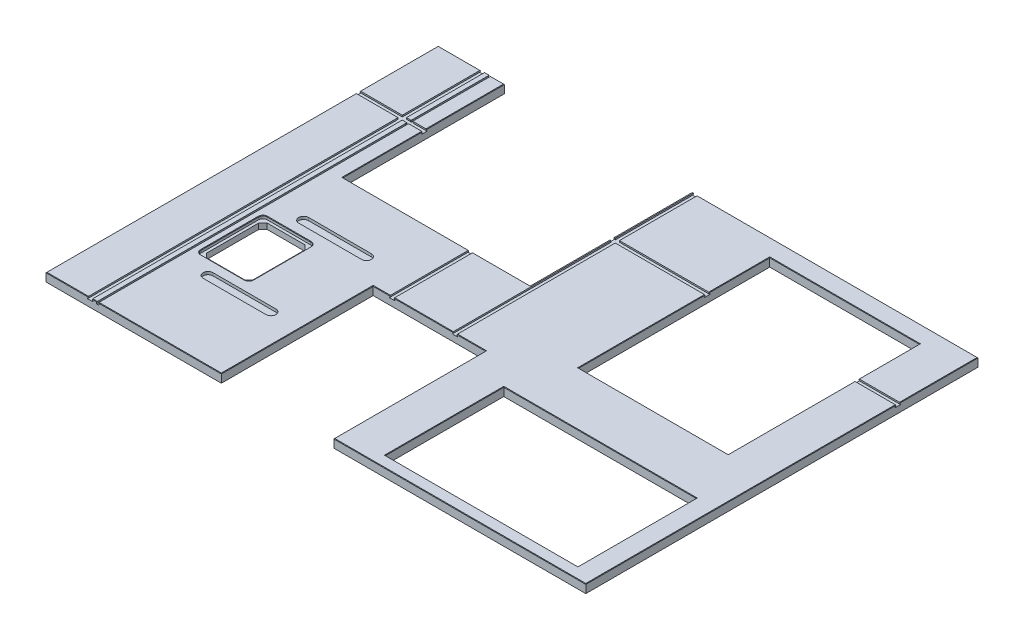
SolidWorks part; units mm, degrees
material "Oak"
ref_plane "Front Plane" through (0, 0, 0) normal (0, 0, 1) x (1, 0, 0)
ref_plane "Top Plane" through (0, 0, 0) normal (0, 1, 0) x (1, 0, 0)
ref_plane "Right Plane" through (0, 0, 0) normal (1, 0, 0) x (0, 0, -1)
sketch "Sketch1" plane through (0, 0, 0) normal (0, 1, 0) x (1, 0, 0)
  line L4 (2438.4, 0) -> (2438.4, 1771.65)
  line L5 (2438.4, 1771.65) -> (0, 1771.65)
  line L7 (0, 0) -> (2438.4, 0)
  line L8 (0, 1771.65) -> (0, 0)
  dimension "D1" = 2438.4
  dimension "D5" = 1771.65
extrude "Boss-Extrude1" add sketch "Sketch1" against normal blind 38.1
sketch "Sketch2" plane through (0, 0, 0) normal (0, 1, 0) x (1, 0, 0)
  line L1 (1482.09, 585.7875) -> (2352.04, 585.7875)
  line L2 (1482.09, 585.7875) -> (1482.09, 50.8)
  line L3 (1482.09, 50.8) -> (2352.04, 50.8)
  line L4 (2352.04, 585.7875) -> (2352.04, 50.8)
  dimension "D1" = 869.95
  dimension "D2" = 534.9875
  dimension "D3" = 1482.09
  dimension "D4" = 50.8
extrude "Cut-Extrude1" cut sketch "Sketch2" against normal through all
sketch "Sketch3" plane through (0, 0, 0) normal (0, 1, 0) x (1, 0, 0)
  line L0 (0, 0) -> (2438.4, 0) construction
  line L1 (792.1625, 685.8) -> (1300.1625, 685.8)
  line L2 (792.1625, 685.8) -> (792.1625, 0)
  line L3 (792.1625, 0) -> (1300.1625, 0)
  line L4 (1300.1625, 685.8) -> (1300.1625, 0)
  dimension "D1" = 508
  dimension "D2" = 792.1625
  dimension "D3" = 685.8
extrude "Cut-Extrude2" cut sketch "Sketch3" against normal through all
sketch "Sketch4" plane through (0, 0, 0) normal (0, 1, 0) x (1, 0, 0)
  line L1 (1576.4256, 1692.91) -> (2252.6269, 1692.91)
  line L2 (1576.4256, 1692.91) -> (1576.4256, 829.0585)
  line L3 (1576.4256, 829.0585) -> (2252.6269, 829.0585)
  line L4 (2252.6269, 1692.91) -> (2252.6269, 829.0585)
  dimension "D1" = 1576.4256
  dimension "D2" = 676.2013
  dimension "D3" = 1692.91
  dimension "D4" = 863.8515
extrude "Cut-Extrude3" cut sketch "Sketch4" against normal through all
sketch "Sketch5" plane through (0, 0, 0) normal (0, 1, 0) x (1, 0, 0)
  line L1 (299.1104, 1771.65) -> (1145.54, 1771.65)
  line L2 (299.1104, 1771.65) -> (299.1104, 1041.4)
  line L3 (299.1104, 1041.4) -> (1145.54, 1041.4)
  line L4 (1145.54, 1771.65) -> (1145.54, 1041.4)
  line L7 (2438.4, 1771.65) -> (0, 1771.65) construction
  dimension "D1" = 299.1104
  dimension "D2" = 846.4296
  dimension "D3" = 1041.4
extrude "Cut-Extrude4" cut sketch "Sketch5" against normal through all
sketch "Sketch7" plane through (0, 0, 0) normal (0, 1, 0) x (1, 0, 0)
  line L1 (281.3685, 717.55) -> (478.2185, 717.55)
  line L2 (262.3185, 698.5) -> (262.3185, 438.15)
  line L3 (281.3685, 419.1) -> (478.2185, 419.1)
  line L4 (497.2685, 698.5) -> (497.2685, 438.15)
  arc A0 (497.2685, 438.15) -> (478.2185, 419.1) centre (478.2185, 438.15) cw
  arc A1 (281.3685, 419.1) -> (262.3185, 438.15) centre (281.3685, 438.15) cw
  arc A2 (262.3185, 698.5) -> (281.3685, 717.55) centre (281.3685, 698.5) cw
  arc A3 (478.2185, 717.55) -> (497.2685, 698.5) centre (478.2185, 698.5) cw
  dimension "D5" = 19.05
  dimension "D1" = 262.3185
  dimension "D2" = 234.95
  dimension "D3" = 419.1
  dimension "D4" = 298.45
extrude "Cut-Extrude5" cut sketch "Sketch7" against normal blind 12.7
sketch "Sketch8" plane through (0, -12.7, 0) normal (0, 1, 0) x (1, 0, 0)
  line L0 (294.0685, 704.85) -> (275.0185, 685.8)
  line L1 (294.0685, 704.85) -> (465.5185, 704.85)
  line L2 (275.0185, 685.8) -> (275.0185, 450.85)
  line L3 (294.0685, 431.8) -> (465.5185, 431.8)
  line L4 (484.5685, 685.8) -> (484.5685, 450.85)
  line L5 (379.7935, 369.414) -> (379.7935, 778.191) construction
  line L6 (219.5895, 568.325) -> (559.0988, 568.325) construction
  line L7 (465.5185, 704.85) -> (484.5685, 685.8)
  line L8 (465.5185, 431.8) -> (484.5685, 450.85)
  line L9 (294.0685, 431.8) -> (275.0185, 450.85)
  point P4 (379.7935, 704.85)
  dimension "D5" = 19.05
  dimension "D1" = 275.0185
  dimension "D2" = 209.55
  dimension "D3" = 431.8
  dimension "D4" = 273.05
  dimension "D6" = 19.05
extrude "Cut-Extrude6" cut sketch "Sketch8" against normal through all
sketch "Sketch10" plane through (0, 0, -685.8) normal (0, 0, 1) x (1, 0, 0)
  line L0 (1161.7833, 41.8774) -> (1161.7833, 25.4484) construction
  line L1 (1152.2583, 0) -> (1171.3083, 0)
  line L2 (1171.3083, 0) -> (1171.3083, -6.0452)
  line L3 (1171.3083, -6.0452) -> (1173.9245, -6.0452)
  line L4 (1173.9245, -6.0452) -> (1173.9245, -9.525)
  line L5 (1173.9245, -9.525) -> (1149.6421, -9.525)
  line L6 (1149.6421, -9.525) -> (1149.6421, -6.0452)
  line L7 (1149.6421, -6.0452) -> (1152.2583, -6.0452)
  line L8 (1152.2583, -6.0452) -> (1152.2583, 0)
  line L11 (877.6081, 37.6795) -> (877.6081, 21.2504) construction
  line L12 (868.0831, 0) -> (887.1331, 0)
  line L13 (887.1331, 0) -> (887.1331, -6.0452)
  line L14 (887.1331, -6.0452) -> (889.7493, -6.0452)
  line L15 (889.7493, -6.0452) -> (889.7493, -9.525)
  line L16 (889.7493, -9.525) -> (865.4669, -9.525)
  line L17 (865.4669, -9.525) -> (865.4669, -6.0452)
  line L18 (865.4669, -6.0452) -> (868.0831, -6.0452)
  line L19 (868.0831, -6.0452) -> (868.0831, 0)
  line L20 (1300.1625, 0) -> (792.1625, 0) construction
  point P3 (1161.7833, -9.525)
  dimension "D1" = 24.2824
  dimension "D2" = 19.05
  dimension "D3" = 9.525
  dimension "D4" = 3.4798
  dimension "D5" = 1161.7833
  dimension "D6" = 24.2824
  dimension "D7" = 19.05
  dimension "D8" = 3.4798
  dimension "D9" = 284.1752
  dimension "D10" = 9.525
extrude "Cut-Extrude7" cut sketch "Sketch10" against normal through all
sketch "Sketch12" plane through (0, 0, 0) normal (0, 0, 1) x (1, 0, 0)
  line L32 (0, 0) -> (792.1625, 0) construction
  line L33 (190.2079, 0) -> (209.2579, 0)
  line L36 (262.3185, -12.7) -> (262.3185, 0) construction
  line L37 (230.0859, 0) -> (237.4519, 0)
  line L40 (120.6953, 34.7588) -> (120.6953, -55.09) construction
  line L41 (199.7329, 11.4165) -> (199.7329, 27.3169) construction
  line L42 (233.7689, -9.525) -> (233.7689, 29.7944) construction
  line L47 (190.2079, -6.096) -> (187.7949, -6.096)
  line L48 (190.2079, 0) -> (190.2079, -6.096)
  line L49 (237.4519, -2.54) -> (237.4519, 0)
  line L50 (239.4839, -2.54) -> (237.4519, -2.54)
  line L51 (239.4839, -9.525) -> (239.4839, -2.54)
  line L52 (228.0539, -9.525) -> (239.4839, -9.525)
  line L53 (228.0539, -2.54) -> (228.0539, -9.525)
  line L54 (230.0859, -2.54) -> (228.0539, -2.54)
  line L55 (230.0859, 0) -> (230.0859, -2.54)
  line L56 (209.2579, -6.096) -> (209.2579, 0)
  line L57 (211.6709, -6.096) -> (209.2579, -6.096)
  line L58 (211.6709, -9.525) -> (211.6709, -6.096)
  line L59 (187.7949, -9.525) -> (211.6709, -9.525)
  line L60 (187.7949, -6.096) -> (187.7949, -9.525)
  point P7 (189.0014, -6.096)
  line M43 (792.1625, 0) -> (0, 0)
  dimension "D2" = 34.036
  dimension "D3" = 2.54
  dimension "D4" = 9.525
  dimension "D5" = 11.43
  dimension "D6" = 7.366
  dimension "D7" = 6.096
  dimension "D9" = 23.876
  dimension "D10" = 19.05
  dimension "D11" = 32.2326
extrude "Cut-Extrude8" cut sketch "Sketch12" against normal through all contours L47 L60 L59 L58 L57 L56 L48 M43 | L55 L54 L53 L52 L51 L50 L49 M43
sketch "Sketch16" plane through (0, 0, 0) normal (-1, 0, 0) x (0, 0, 1)
  line L0 (-1771.65, 0) -> (0, 0) construction
  line L1 (-1421.892, -9.525) -> (-1397.508, -9.525)
  line L2 (-1421.892, -9.525) -> (-1421.892, -5.969)
  line L3 (-1421.892, -5.969) -> (-1419.225, -5.969)
  line L4 (-1397.508, -9.525) -> (-1397.508, -5.969)
  line L5 (-1419.225, 0) -> (-1400.175, 0)
  line L6 (-1419.225, 0) -> (-1419.225, -5.969)
  line L8 (-1400.175, 0) -> (-1400.175, -5.969)
  line L9 (-1409.7, -26.666) -> (-1409.7, 16.3649) construction
  line L10 (-1400.175, -5.969) -> (-1397.508, -5.969)
  line L12 (-1041.4, -38.1) -> (-1041.4, 0) construction
  dimension "D1" = 358.775
  dimension "D2" = 24.384
  dimension "D3" = 19.05
  dimension "D4" = 5.969
  dimension "D5" = 9.525
extrude "Cut-Extrude10" cut sketch "Sketch16" against normal through all
chamfer "Chamfer4" distance 2.032 angle 45 37 edges at (1016.3365, 0, -1041.4) (1019.6957, 0, -685.8) (830.1228, 0, -685.8) (219.6719, 0, 0) (514.8072, 0, 0) (2352.04, 0, -318.2937) (1917.065, 0, -585.7875) (1482.09, 0, -318.2937) (1917.065, 0, -50.8) (1145.54, 0, -1595.4375) (299.1104, 0, -1220.7875) (1576.4256, 0, -1114.6168) (2252.6269, 0, -1556.0675) (1869.2813, 0, 0) (2438.4, 0, -1595.4375) (0, 0, -700.0875) (792.1625, 0, -342.9) (1300.1625, 0, -342.9) (1235.7354, 0, -685.8) (0, 0, -1595.4375) (2252.6269, 0, -1114.6168) (1914.5263, 0, -1692.91) (1576.4256, 0, -1556.0675) (1914.5263, 0, -829.0585) (2438.4, 0, -700.0875) (95.1039, 0, 0) (299.1104, 0, -1595.4375) (583.5967, 0, -1041.4) (1145.54, 0, -1220.7875) (491.6889, 0, -424.6796) (497.2685, 0, -568.325) (491.6889, 0, -711.9704) (379.7935, 0, -717.55) (267.8981, 0, -711.9704) (262.3185, 0, -568.325) (267.8981, 0, -424.6796) (379.7935, 0, -419.1)
sketch "Sketch17" plane through (0, 0, 0) normal (0, 1, 0) x (1, 0, 0)
  line L4 (378.5304, 763.0422) -> (662.4636, 763.0422)
  line L5 (662.4636, 807.4844) -> (378.5304, 807.4844)
  line L6 (378.7742, 331.3021) -> (662.4636, 331.3021)
  line L7 (662.4636, 375.7444) -> (378.5304, 375.7444)
  line L8 (378.5304, 785.2633) -> (662.4636, 785.2633) construction
  line L9 (662.4636, 785.2633) -> (662.4636, 353.5233) construction
  line L10 (662.4636, 353.5233) -> (378.5304, 353.5233) construction
  line L11 (378.5304, 353.5233) -> (378.5304, 785.2633) construction
  line L12 (438.4679, 568.325) -> (587.5673, 568.325) construction
  line L13 (294.0685, 431.8) -> (465.5185, 431.8) construction
  line L14 (465.5185, 704.85) -> (294.0685, 704.85) construction
  line L15 (499.3005, 698.5) -> (499.3005, 438.15) construction
  arc A1 (662.4636, 331.3021) -> (662.4636, 375.7444) centre (662.4636, 353.5233) ccw
  arc A2 (378.5304, 375.7444) -> (378.5304, 331.3021) centre (378.5304, 353.5233) ccw
  arc A3 (662.4636, 763.0422) -> (662.4636, 807.4844) centre (662.4636, 785.2633) ccw
  arc A4 (378.5304, 807.4844) -> (378.5304, 763.0422) centre (378.5304, 785.2633) ccw
  dimension "D6" = 43.4602
  dimension "D3" = 22.2211
  dimension "D1" = 283.9332
  dimension "D2" = 431.74
  dimension "D4" = 163.1631
  dimension "D5" = 120.5263
extrude "Cut-Extrude12" cut sketch "Sketch17" against normal blind 12.7 contours L5 A4 L4 A3 | L6 A1 L7 A2
sketch "Sketch18" plane through (0, 0, 0) normal (0, 1, 0) x (1, 0, 0)
  line L0 (378.5304, 353.4633) -> (662.4636, 353.4633) construction
  line L1 (378.5304, 375.6844) -> (662.4636, 375.6844)
  line L2 (378.5304, 331.2422) -> (662.4636, 331.2422)
  line L3 (378.5304, 763.0422) -> (662.4636, 763.0422) construction
  line L4 (662.4636, 785.2633) -> (378.5304, 785.2633) construction
  line L5 (378.5304, 785.2633) -> (378.5304, 353.4633) construction
  arc A0 (378.5304, 375.6844) -> (378.5304, 331.2422) centre (378.5304, 353.4633) ccw
  arc A1 (662.4636, 331.2422) -> (662.4636, 375.6844) centre (662.4636, 353.4633) ccw
  arc A2 (662.4636, 763.0422) -> (662.4636, 807.4844) centre (662.4636, 785.2633) ccw construction
  point P2 (520.497, 353.4633)
  dimension "D1" = 431.8
extrude "Cut-Extrude13" cut sketch "Sketch18" against normal blind 12.7
